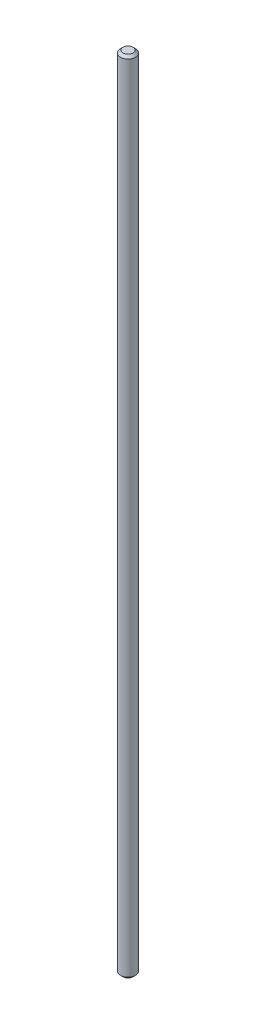
SolidWorks part; units mm, degrees
ref_plane "Спереди" through (0, 0, 0) normal (0, 0, 1) x (1, 0, 0)
ref_plane "Сверху" through (0, 0, 0) normal (0, 1, 0) x (1, 0, 0)
ref_plane "Справа" through (0, 0, 0) normal (1, 0, 0) x (0, 0, -1)
sketch "Эскиз1" plane through (0, 0, 0) normal (0, 1, 0) x (1, 0, 0)
  circle A0 centre (0, 0) radius 3
  dimension "D1" = 6
extrude "Бобышка-Вытянуть1" add sketch "Эскиз1" along normal blind 320
chamfer "Фаска1" distance 1 angle 45 1 edges at (0, 320, 3)
chamfer "Фаска2" distance 1 angle 45 1 edges at (0, 0, 3)
